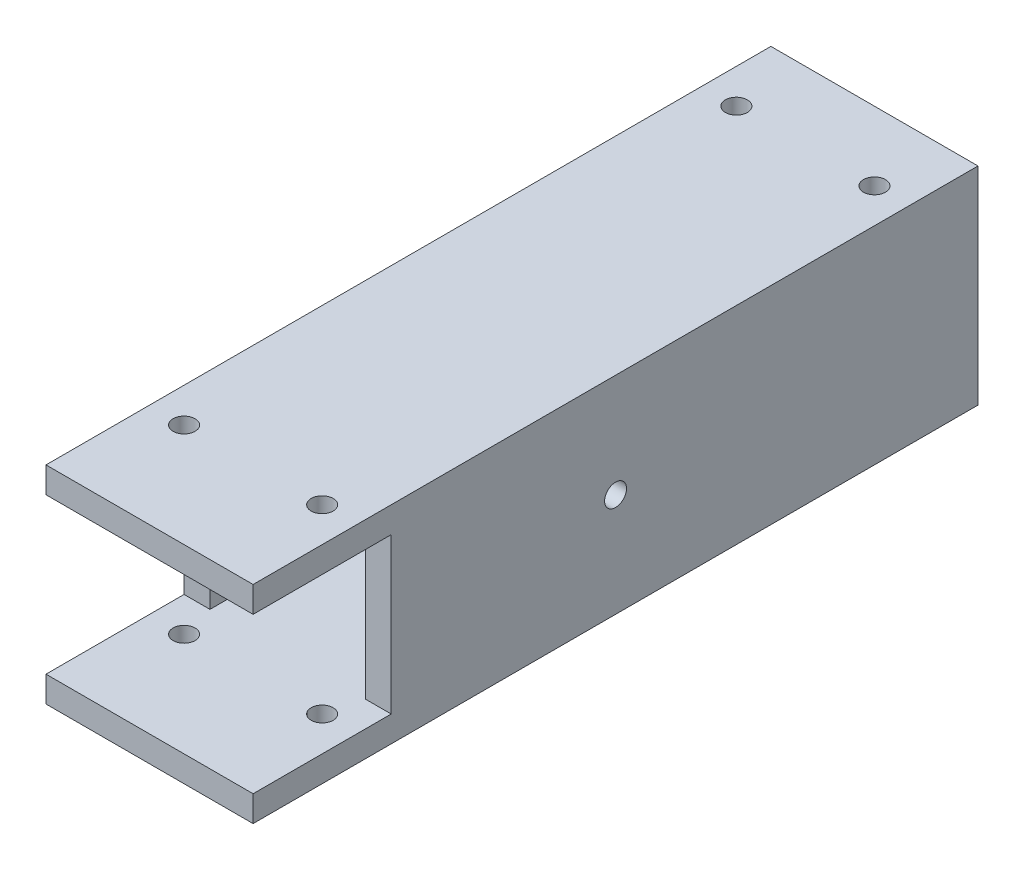
SolidWorks part; units mm, degrees
material "6061 Alloy"
ref_plane "Front Plane" through (0, 0, 0) normal (0, 0, 1) x (1, 0, 0)
ref_plane "Top Plane" through (0, 0, 0) normal (0, 1, 0) x (1, 0, 0)
ref_plane "Right Plane" through (0, 0, 0) normal (1, 0, 0) x (0, 0, -1)
sketch "Sketch1" plane through (0, 0, 0) normal (0, 1, 0) x (1, 0, 0)
  line L1 (-19.05, 66.675) -> (19.05, 66.675)
  line L2 (-19.05, 66.675) -> (-19.05, -66.675)
  line L3 (-19.05, -66.675) -> (19.05, -66.675)
  line L4 (19.05, 66.675) -> (19.05, -66.675)
  dimension "D1" = 19.05
  dimension "D2" = 19.05
  dimension "D3" = 66.675
  dimension "D4" = 66.675
extrude "Boss-Extrude1" add sketch "Sketch1" along normal mid plane 38.1
sketch "Sketch2" plane through (0, 0, 66.675) normal (0, 0, 1) x (1, 0, 0)
  line L0 (-19.05, 19.05) -> (-19.05, -19.05) construction
  line L1 (-14.2875, 14.2875) -> (14.2875, 14.2875)
  line L2 (-14.2875, 14.2875) -> (-14.2875, -14.2875)
  line L3 (-14.2875, -14.2875) -> (14.2875, -14.2875)
  line L4 (14.2875, 14.2875) -> (14.2875, -14.2875)
  line L5 (19.05, 19.05) -> (19.05, -19.05) construction
  line L6 (-19.05, -19.05) -> (19.05, -19.05) construction
  line L7 (-19.05, 19.05) -> (19.05, 19.05) construction
  dimension "D1" = 4.7625
  dimension "D2" = 4.7625
  dimension "D3" = 4.7625
  dimension "D4" = 4.7625
extrude "Cut-Extrude1" cut sketch "Sketch2" against normal through all
sketch "Sketch3" plane through (19.05, 0, 0) normal (1, 0, 0) x (0, 0, -1)
  line L0 (-66.675, 19.05) -> (-66.675, -19.05) construction
  line L1 (-66.675, 14.2875) -> (-41.275, 14.2875)
  line L2 (-66.675, 14.2875) -> (-66.675, -14.2875)
  line L3 (-66.675, -14.2875) -> (-41.275, -14.2875)
  line L4 (-41.275, 14.2875) -> (-41.275, -14.2875)
  line L5 (-66.675, -19.05) -> (66.675, -19.05) construction
  line L6 (-66.675, 19.05) -> (66.675, 19.05) construction
  dimension "D1" = 25.4
  dimension "D2" = 4.7625
  dimension "D3" = 4.7625
extrude "Cut-Extrude2" cut sketch "Sketch3" against normal through all
hole_wizard "#10-32 Tapped Hole1" positions "Sketch5" profile "Sketch4" tap size "#10-32" standard "ANSI Inch"
sketch "Sketch5" plane through (0, 19.05, 0) normal (0, 1, 0) x (1, 0, 0)
  line L0 (-19.05, -66.675) -> (19.05, -66.675) construction
  line L1 (19.05, 66.675) -> (-19.05, 66.675) construction
  point P0 (-12.7, -47.625)
  point P2 (12.7, -47.625)
  point P4 (-12.7, 53.975)
  point P6 (12.7, 53.975)
  dimension "D1" = 19.05
  dimension "D2" = 12.7
  dimension "D3" = 12.7
  dimension "D4" = 12.7
sketch "Sketch4" plane through (-12.7, 19.05, 47.625) normal (1, 0, 0) x (0, 0, 1)
  line L0 (0, 0) -> (0, 12.3893)
  line L1 (0, 12.3893) -> (2.0193, 11.176)
  line L2 (2.0193, 11.176) -> (2.0193, 0)
  line L5 (2.0193, 0) -> (0, 0)
  line L10 (0, 12.3893) -> (-2.0193, 11.176) construction
  line L11 (0, -6.35) -> (0, 107.95) construction
  dimension "Tap Drill Dia." = 4.0386
  dimension "Tap Drill Depth" = 11.176
  dimension "Drill Angle" = 118
cosmetic thread "Hole Thread1" parameters "D1"=3.175, "D2"=4.826
cosmetic thread "Hole Thread2" parameters "D1"=3.175, "D2"=4.826
cosmetic thread "Hole Thread3" parameters "D1"=3.175, "D2"=4.826
cosmetic thread "Hole Thread4" parameters "D1"=3.175, "D2"=4.826
hole_wizard "#10-32 Tapped Hole2" positions "Sketch7" profile "Sketch6" tap size "#10-32" standard "ANSI Inch" end condition through all
sketch "Sketch7" plane through (19.05, 0, 0) normal (1, 0, 0) x (0, 0, -1)
  point P0 (0, 0)
sketch "Sketch6" plane through (19.05, 0, 0) normal (0, 1, 0) x (0, 0, -1)
  line L0 (0, 0) -> (0, 38.1)
  line L1 (0, 38.1) -> (2.0193, 38.1)
  line L2 (2.0193, 38.1) -> (2.0193, 0)
  line L5 (2.0193, 0) -> (0, 0)
  line L11 (0, -6.35) -> (0, 107.95) construction
  dimension "Thru Tap Drill Dia." = 4.0386
  dimension "Thru Tap Drill Depth" = 38.1
cosmetic thread "Hole Thread5" parameters "D2"=4.826
mirror "Mirror1" about plane through (0, 0, 0) normal (0, 1, 0) of "#10-32 Tapped Hole1"
